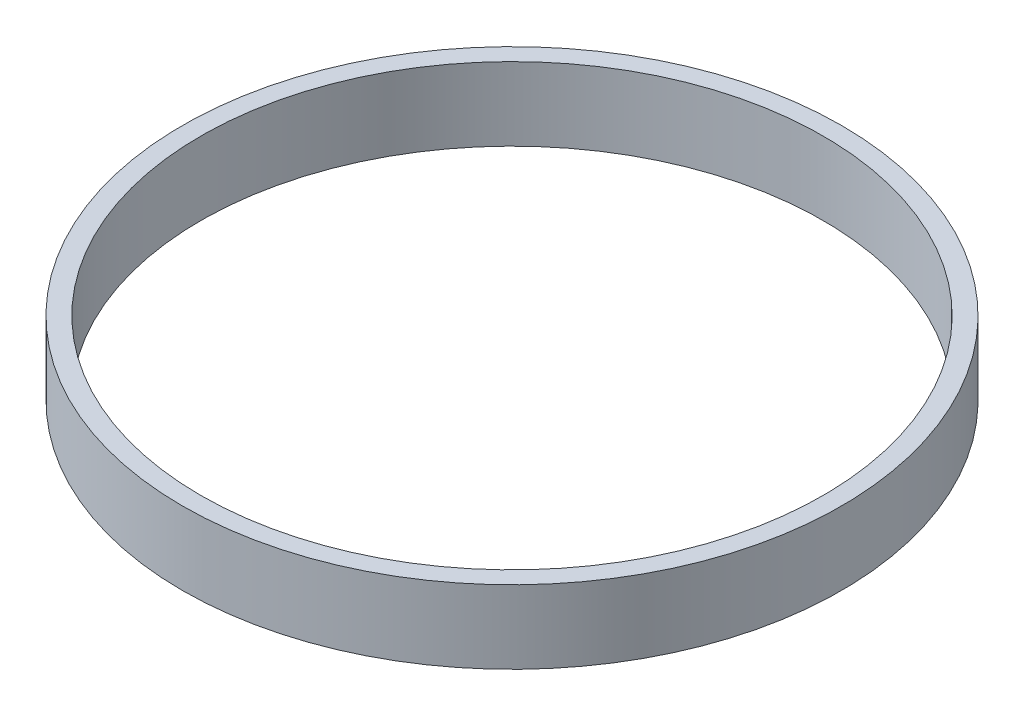
SolidWorks part; units mm, degrees
material "PP Copolymer"
ref_plane "Front Plane" through (0, 0, 0) normal (0, 0, 1) x (1, 0, 0)
ref_plane "Top Plane" through (0, 0, 0) normal (0, 1, 0) x (1, 0, 0)
ref_plane "Right Plane" through (0, 0, 0) normal (1, 0, 0) x (0, 0, -1)
sketch "Sketch1" plane through (0, 0, 0) normal (0, 1, 0) x (1, 0, 0)
  circle A0 centre (0, 0) radius 45
  dimension "D1" = 90
extrude "Boss-Extrude1" add sketch "Sketch1" along normal blind 10
sketch "Sketch3" plane through (0, 10, 0) normal (0, 1, 0) x (1, 0, 0)
  circle A0 centre (0, 0) radius 42.5
  dimension "D1" = 85
extrude "Cut-Extrude1" cut sketch "Sketch3" against normal blind 20.35
